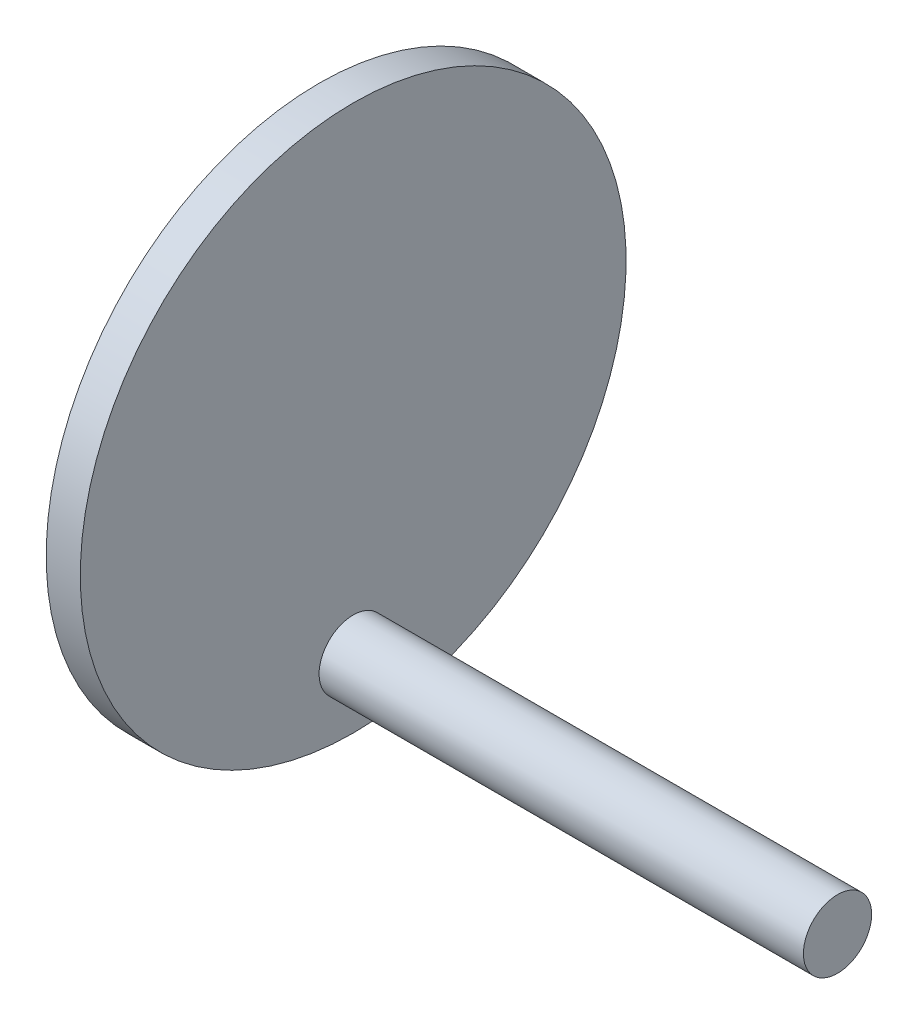
SolidWorks part; units mm, degrees
ref_plane "Front Plane" through (0, 0, 0) normal (0, 0, 1) x (1, 0, 0)
ref_plane "Top Plane" through (0, 0, 0) normal (0, 1, 0) x (1, 0, 0)
ref_plane "Right Plane" through (0, 0, 0) normal (1, 0, 0) x (0, 0, -1)
sketch "Sketch2" plane through (10, 0, 0) normal (1, 0, 0) x (0, 0, -1)
  line L0 (-57.5, 10) -> (57.5, 10) construction
  line L1 (-57.5, 10) -> (-57.5, 150) construction
  circle A0 centre (0, 60) radius 7.5
  dimension "D1" = 15
  dimension "D2" = 50
  dimension "D3" = 57.5
extrude "Boss-Extrude1" add sketch "Sketch2" along normal blind 5 and the other way blind 15
sketch "Sketch3" plane through (15, 0, 0) normal (1, 0, 0) x (0, 0, -1)
  circle A0 centre (0, 60) radius 40
  dimension "D1" = 80
extrude "Boss-Extrude2" add sketch "Sketch3" along normal blind 5
sketch "Sketch4" plane through (20, 0, 0) normal (1, 0, 0) x (0, 0, -1)
  line L0 (0, 60) -> (0, 30) construction
  circle A0 centre (0, 30) radius 5
  dimension "D1" = 10
  dimension "D2" = 30
extrude "Boss-Extrude3" add sketch "Sketch4" along normal blind 70.9881
